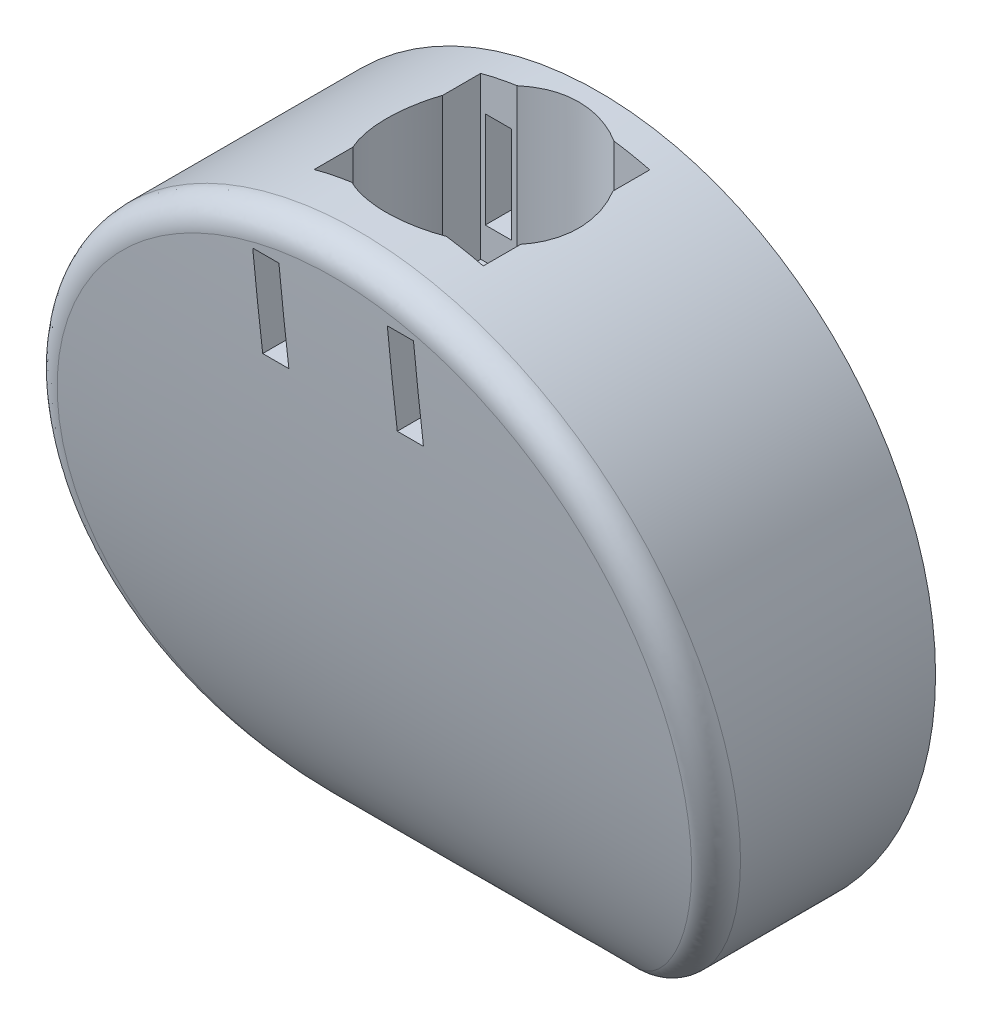
SolidWorks part; units mm, degrees
ref_plane "Plan de face" through (0, 0, 0) normal (0, 0, 1) x (1, 0, 0)
ref_plane "Plan de dessus" through (0, 0, 0) normal (0, 1, 0) x (1, 0, 0)
ref_plane "Plan de droite" through (0, 0, 0) normal (1, 0, 0) x (0, 0, -1)
sketch "Esquisse1" plane through (0, 0, 0) normal (0, 0, 1) x (1, 0, 0)
  circle A0 centre (0.2907, 0.2907) radius 67
  dimension "D1" = 134
extrude "Boss.-Extru.1" add sketch "Esquisse1" along normal blind 53.34
sketch "Esquisse4" plane through (0, 0, 0) normal (1, 0, 0) x (0, 0, -1)
  line L1 (-0.1422, -67.1272) -> (-53.34, -66.7093)
  line L2 (-53.34, -66.7093) -> (-53.34, 67.2907)
  spline S0 degree 3 poles (-53.34, 67.2907) (-53.3149, 64.9653) (-44.6519, -34.8903) (-23.1604, -66.3734) (-0.1422, -67.1272) knots 0 0 0 0 0.36297 1 1 1 1
extrude "Enlèv. mat.-Extru.1" cut sketch "Esquisse4" against normal through all both and the other way through all
fillet "Congé1" radius 5 1 edges at (-0.0427, -66.7085, 4.6747)
ref_plane "Plan2" through (0, 67.2907, 0) normal (0, 1, 0) x (1, 0, 0)
sketch "Esquisse6" plane through (0, 67.2907, 0) normal (0, 1, 0) x (1, 0, 0)
  line L0 (67.2907, 0) -> (-66.7093, 0) construction
  line L1 (-16.9103, -6.35) -> (-9.6498, -6.35)
  line L2 (-16.9103, -6.35) -> (-16.9103, -13.9146)
  line L3 (-16.9103, -39.497) -> (-9.4287, -39.497)
  line L4 (16.7447, -6.35) -> (16.7447, -13.6788)
  line L5 (67.2907, -40.0395) -> (67.2907, 0) construction
  line L6 (-16.9103, -31.8054) -> (-16.9103, -39.497)
  line L7 (9.3901, -39.497) -> (16.7447, -39.497)
  line L8 (16.7447, -32.0412) -> (16.7447, -39.497)
  line L9 (9.6112, -6.35) -> (16.7447, -6.35)
  arc A0 (-16.9103, -13.9146) -> (-16.9103, -31.8054) centre (-0.0193, -22.86) ccw
  arc A1 (-9.4287, -39.497) -> (9.3901, -39.497) centre (-0.0193, -22.86) ccw
  arc A2 (16.7447, -32.0412) -> (16.7447, -13.6788) centre (-0.0193, -22.86) ccw
  arc A3 (9.6112, -6.35) -> (-9.6498, -6.35) centre (-0.0193, -22.86) ccw
  dimension "D5" = 38.227
  dimension "D1" = 33.655
  dimension "D2" = 33.147
  dimension "D3" = 22.86
  dimension "D4" = 67.31
  dimension "D6" = 16.51
  dimension "D7" = 16.764
extrude "Enlèv. mat.-Extru.4" cut sketch "Esquisse6" against normal blind 34.29
ref_plane "Plan4" through (0, 0, 6.35) normal (0, 0, 1) x (1, 0, 0)
sketch "Esquisse10" plane through (0, 0, 6.35) normal (0, 0, 1) x (1, 0, 0)
  line L1 (-15.9998, 58.5277) -> (-10.7928, 58.5277)
  line L2 (-15.9998, 58.5277) -> (-15.9998, 39.3507)
  line L3 (-15.9998, 39.3507) -> (-10.7928, 39.3507)
  line L4 (-10.7928, 58.5277) -> (-10.7928, 39.3507)
  line L5 (-9.6498, 33.0007) -> (-9.6498, 66.5492) construction
  line L7 (-9.6498, 33.0007) -> (-16.9103, 33.0007) construction
  dimension "D1" = 5.207
  dimension "D2" = 19.177
  dimension "D3" = 1.143
  dimension "D4" = 6.35
extrude "Enlèv. mat.-Extru.7" cut sketch "Esquisse10" against normal through all
mirror "Symétrie1" about plane through (0, 0, 0) normal (1, 0, 0) of "Enlèv. mat.-Extru.7"
ref_plane "Plan5" through (0, 0, 22.8611) normal (0, 0, -1) x (-1, 0, 0)
mirror "Symétrie2" about plane through (0, 0, 22.8611) normal (0, 0, -1) of "Symétrie1", "Enlèv. mat.-Extru.7"
sketch "Esquisse12" [suppressed] plane through (15.7461, 0, 0) normal (-1, 0, 0) x (0, 0, 1)
  line L0 (52.6258, 58.4007) -> (50.6529, 39.3507)
  line L1 (50.6529, 39.3507) -> (39.37, 39.3507)
  line L2 (39.37, 39.3507) -> (39.37, 58.4007)
  line L3 (39.37, 58.4007) -> (52.6258, 58.4007)
  line L4 (52.6258, 58.4007) -> (39.37, 58.4007) construction
  line L5 (50.6529, 39.3507) -> (39.37, 39.3507) construction
ref_plane "Plan6" through (0, 35.5407, 0) normal (0, 1, 0) x (1, 0, 0)
sketch "Esquisse7" plane through (0, 35.5407, 0) normal (0, 1, 0) x (1, 0, 0)
  circle A0 centre (-0.0193, -22.86) radius 7.62
  arc A1 (9.6112, -6.35) -> (-9.6498, -6.35) centre (-0.0193, -22.86) ccw construction
  dimension "D1" = 15.24
extrude "Enlèv. mat.-Extru.8" cut sketch "Esquisse7" against normal blind 6.35
